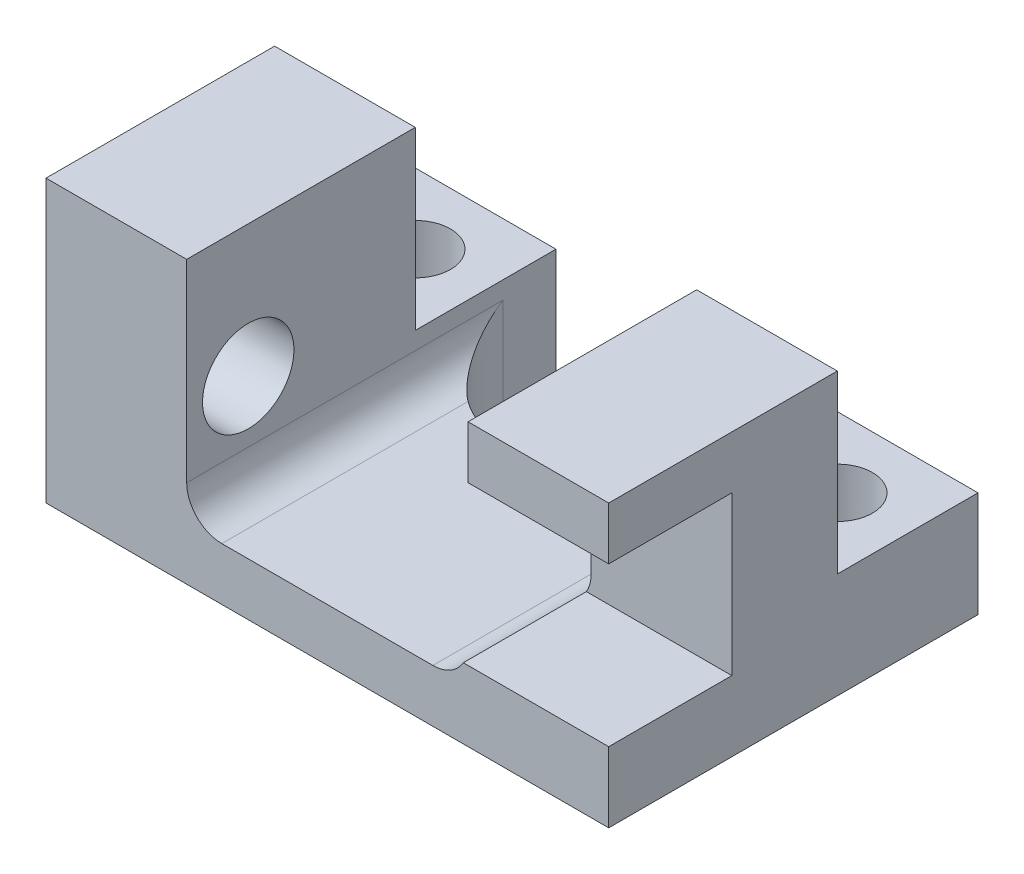
SolidWorks part; units mm, degrees
ref_plane "Front Plane" through (0, 0, 0) normal (0, 0, 1) x (1, 0, 0)
ref_plane "Top Plane" through (0, 0, 0) normal (0, 1, 0) x (1, 0, 0)
ref_plane "Right Plane" through (0, 0, 0) normal (1, 0, 0) x (0, 0, -1)
sketch "Sketch1" plane through (0, 0, 0) normal (0, 1, 0) x (1, 0, 0)
  line L1 (-8, -3.25) -> (8, -3.25)
  line L2 (-8, -3.25) -> (-8, 3.25)
  line L3 (-8, 3.25) -> (8, 3.25)
  line L4 (8, -3.25) -> (8, 3.25)
  line L5 (-8, -3.25) -> (8, 3.25) construction
  line L6 (-8, 3.25) -> (8, -3.25) construction
  point P0 (0, 0)
  dimension "D1" = 6.5
  dimension "D2" = 16
extrude "Boss-Extrude1" add sketch "Sketch1" along normal mid plane 8
sketch "Sketch2" plane through (0, 4, 5) normal (0, -1, 0) x (1, 0, 0)
  line L0 (8, -8.25) -> (-8, -8.25) construction
  line L1 (-4, -1.75) -> (4, -1.75)
  line L2 (-4, -1.75) -> (-4, -8.25)
  line L3 (-4, -8.25) -> (4, -8.25)
  line L4 (4, -1.75) -> (4, -8.25)
  line L5 (-4, -1.75) -> (4, -8.25) construction
  line L6 (-4, -8.25) -> (4, -1.75) construction
  line L7 (-8, -8.25) -> (-8, -1.75) construction
  point P0 (0, -5)
  dimension "D1" = 4
extrude "Cut-Extrude1" cut sketch "Sketch2" along normal blind 6.5
sketch "Sketch3" plane through (-8, 0, 0) normal (-1, 0, 0) x (0, 0, 1)
  line L0 (-3.25, 4) -> (3.25, 4) construction
  line L5 (3.25, 4) -> (3.25, -4) construction
  line L20 (-0.25, 2.5) -> (3.25, 2.5)
  line L21 (-0.25, 2.5) -> (-0.25, -2)
  line L22 (-0.25, -2) -> (3.25, -2)
  line L23 (3.25, 2.5) -> (3.25, -2)
  line L24 (1.5, -2) -> (1.5, 2.5) construction
  dimension "D1" = 4.5
  dimension "D2" = 1.5
  dimension "D3" = 3.5
extrude "Cut-Extrude2" [suppressed] cut sketch "Sketch3" against normal up to surface (4 mm away)
sketch "Sketch7" plane through (8, 0, 0) normal (1, 0, 0) x (0, 0, -1)
  line L0 (-3.25, 4) -> (3.25, 4) construction
  line L3 (-1.5, -2) -> (-1.5, 2.5) construction
  point P0 (-1.5, 0.25)
  dimension "D1" = 3.75
hole_wizard "M2 Clearance Hole2" [suppressed] positions "Sketch8" profile "Sketch9" hole size "M2" standard "ISO"
sketch "Sketch8" plane through (8, 0, 0) normal (1, 0, 0) x (0, 0, -1)
  point P0 (-1.5, 0.25)
sketch "Sketch9" plane through (8, 0.25, 1.5) normal (0, 1, 0) x (0, 0, -1)
  line L0 (0, 0) -> (0, 4.7811)
  line L1 (0, 4.7811) -> (1.3, 4)
  line L2 (1.3, 4) -> (1.3, 0)
  line L5 (1.3, 0) -> (0, 0)
  line L10 (0, 4.7811) -> (-1.3, 4) construction
  line L11 (0, -6.35) -> (0, 107.95) construction
  dimension "Hole Dia." = 2.6
  dimension "Hole Depth" = 4
  dimension "Drill Angle" = 118
sketch "Sketch10" plane through (0, -4, 0) normal (0, -1, 0) x (1, 0, 0)
  line L1 (8, -3.25) -> (4, -3.25)
  line L2 (8, -3.25) -> (8, -7.25)
  line L3 (8, -7.25) -> (4, -7.25)
  line L4 (4, -3.25) -> (4, -7.25)
  line L5 (-8, -3.25) -> (-4, -3.25)
  line L6 (-8, -3.25) -> (-8, -7.25)
  line L7 (-8, -7.25) -> (-4, -7.25)
  line L8 (-4, -3.25) -> (-4, -7.25)
  dimension "D1" = 4
  dimension "D2" = 4
extrude "Boss-Extrude2" add sketch "Sketch10" against normal blind 3
sketch "Sketch11" plane through (0, -1, 0) normal (0, 1, 0) x (1, 0, 0)
  line L0 (4, 7.25) -> (8, 7.25) construction
  line L1 (-8, 7.25) -> (-4, 7.25) construction
  line L2 (8, 7.25) -> (8, 3.25) construction
  point P0 (6, 5.25)
  point P1 (-6, 5.25)
  point P5 (6, 7.25)
  point P9 (-6, 7.25)
  point P12 (8, 5.25)
hole_wizard "M1.6 Clearance Hole1" positions "Sketch12" profile "Sketch13" hole size "M1.6" standard "ISO"
sketch "Sketch12" plane through (0, -1, 0) normal (0, 1, 0) x (1, 0, 0)
  point P0 (6, 5.25)
  point P3 (-6, 5.25)
sketch "Sketch13" plane through (6, -1, -5.25) normal (1, 0, 0) x (0, 0, 1)
  line L0 (0, 0) -> (0, 4.6009)
  line L1 (0, 4.6009) -> (1, 4)
  line L2 (1, 4) -> (1, 0)
  line L5 (1, 0) -> (0, 0)
  line L10 (0, 4.6009) -> (-1, 4) construction
  line L11 (0, -6.35) -> (0, 107.95) construction
  dimension "Hole Dia." = 2
  dimension "Hole Depth" = 4
  dimension "Drill Angle" = 118
fillet "Fillet1" radius 1 2 edges at (-4, -2.5, 0) (4, -2.5, 0)
fillet "Fillet2" radius 2.5 2 edges at (-4, -2.75, -3.25) (4, -2.75, -3.25)
sketch "Sketch14" plane through (8, 0, 0) normal (1, 0, 0) x (0, 0, -1)
  line L0 (0.25, 2.5) -> (-3.25, 2.5) construction
  line L1 (0.25, 2.5) -> (-3.25, 2.5)
  line L2 (-1.5, -2) -> (-1.5, 2.5) construction
  line L3 (-3.25, 2.5) -> (-3.25, -2) construction
  line L4 (0.25, -2) -> (-3.25, -2) construction
  line L5 (0.25, 2.5) -> (0.25, -2) construction
  line L6 (-1.5, -2) -> (-1.5, 2.5) construction
  line L7 (-3.25, 2.5) -> (-3.25, -2)
  line L8 (0.25, -2) -> (-3.25, -2)
  line L9 (0.25, 2.5) -> (0.25, -2)
extrude "Cut-Extrude3" cut sketch "Sketch14" against normal blind 5
sketch "Sketch15" plane through (-8, 0, 0) normal (-1, 0, 0) x (0, 0, 1)
  point P0 (1.5, 0.25)
hole_wizard "M2 Clearance Hole3" positions "Sketch16" profile "Sketch17" hole size "M2" standard "ISO"
sketch "Sketch16" plane through (-8, 0, 0) normal (-1, 0, 0) x (0, 0, 1)
  point P0 (1.5, 0.25)
sketch "Sketch17" plane through (-8, 0.25, 1.5) normal (0, 1, 0) x (0, 0, 1)
  line L0 (0, 0) -> (0, 4.7811)
  line L1 (0, 4.7811) -> (1.3, 4)
  line L2 (1.3, 4) -> (1.3, 0)
  line L5 (1.3, 0) -> (0, 0)
  line L10 (0, 4.7811) -> (-1.3, 4) construction
  line L11 (0, -6.35) -> (0, 107.95) construction
  dimension "Hole Dia." = 2.6
  dimension "Hole Depth" = 4
  dimension "Drill Angle" = 118
